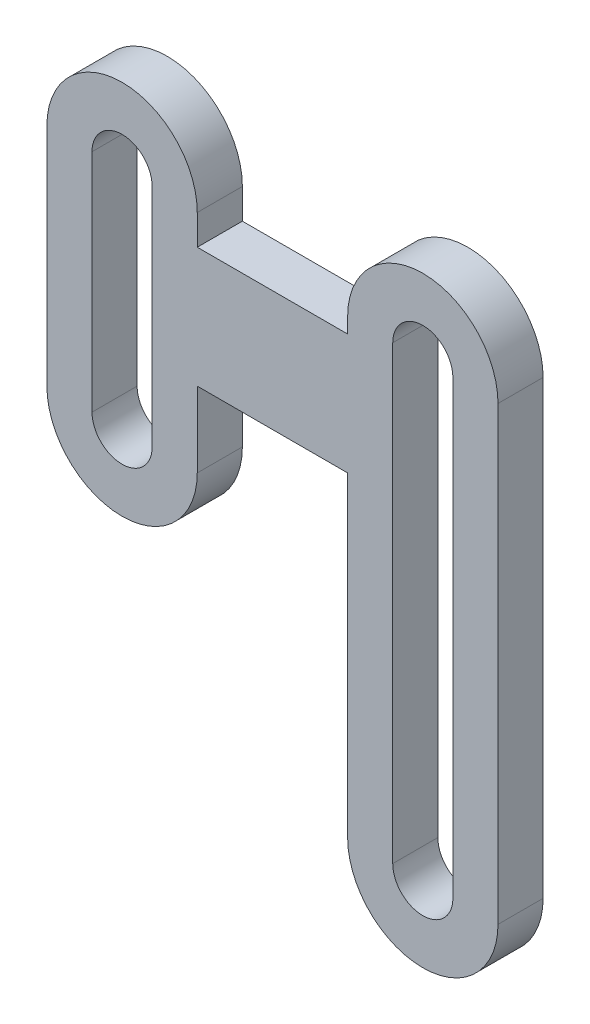
SolidWorks part; units mm, degrees
ref_plane "Plano frontal" through (0, 0, 0) normal (0, 0, 1) x (1, 0, 0)
ref_plane "Plano superior" through (0, 0, 0) normal (0, 1, 0) x (1, 0, 0)
ref_plane "Plano direito" through (0, 0, 0) normal (1, 0, 0) x (0, 0, -1)
sketch "Esboço1" plane through (0, 0, 0) normal (0, 0, 1) x (1, 0, 0)
  line L0 (0, 0) -> (0, 30) construction
  line L1 (-5, 15) -> (-5, 30)
  line L2 (5, 15) -> (5, 20)
  line L3 (20, -1) -> (20, 29) construction
  line L4 (0, 30) -> (0, 15) construction
  line L5 (15, -1) -> (15, 20)
  line L6 (25, -1) -> (25, 29)
  line L7 (2, 30) -> (2, 15)
  line L8 (-2, 30) -> (-2, 15)
  line L9 (15, 28) -> (15, 29)
  line L10 (20, 29) -> (20, -1) construction
  line L11 (22, 29) -> (22, -1)
  line L12 (5, 28) -> (15, 28)
  line L13 (18, 29) -> (18, -1)
  line L15 (5, 20) -> (15, 20)
  line L18 (3.6571, 24) -> (20, 24) construction
  line L19 (5, 28) -> (5, 30)
  arc A0 (15, -1) -> (25, -1) centre (20, -1) ccw
  arc A1 (5, 30) -> (-5, 30) centre (0, 30) ccw
  arc A2 (2, 30) -> (-2, 30) centre (0, 30) ccw
  arc A3 (25, 29) -> (15, 29) centre (20, 29) ccw
  arc A4 (-2, 15) -> (2, 15) centre (0, 15) ccw
  arc A5 (22, 29) -> (18, 29) centre (20, 29) ccw
  arc A6 (18, -1) -> (22, -1) centre (20, -1) ccw
  arc A7 (5, 15) -> (-5, 15) centre (0, 15) cw
  point P2 (0, 0)
  point P6 (0, 22.5)
  point P10 (21, -15.2857)
  point P12 (19.2778, 17.1926)
  point P20 (20, 14)
  point P25 (20.0738, 23.0209)
  dimension "D3" = 5
  dimension "D5" = 2
  dimension "D6" = 30
  dimension "D7" = 1
  dimension "D2" = 30
  dimension "D4" = 15
  dimension "D8" = 10
  dimension "D9" = 5
  dimension "D10" = 8
extrude "Ressalto-extrusão1" add sketch "Esboço1" along normal blind 3
